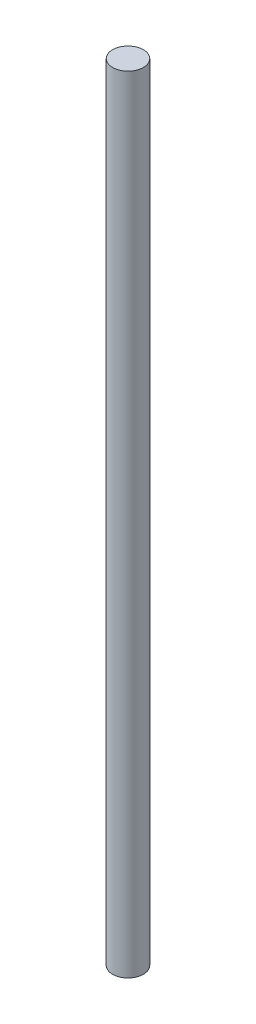
SolidWorks part; units mm, degrees
ref_plane "Front Plane" through (0, 0, 0) normal (0, 0, 1) x (1, 0, 0)
ref_plane "Top Plane" through (0, 0, 0) normal (0, 1, 0) x (1, 0, 0)
ref_plane "Right Plane" through (0, 0, 0) normal (1, 0, 0) x (0, 0, -1)
sketch "Sketch1" plane through (0, 0, 0) normal (0, 1, 0) x (1, 0, 0)
  circle A0 centre (0, 0) radius 3
extrude "Boss-Extrude1" add sketch "Sketch1" along normal blind 153 contours A0
